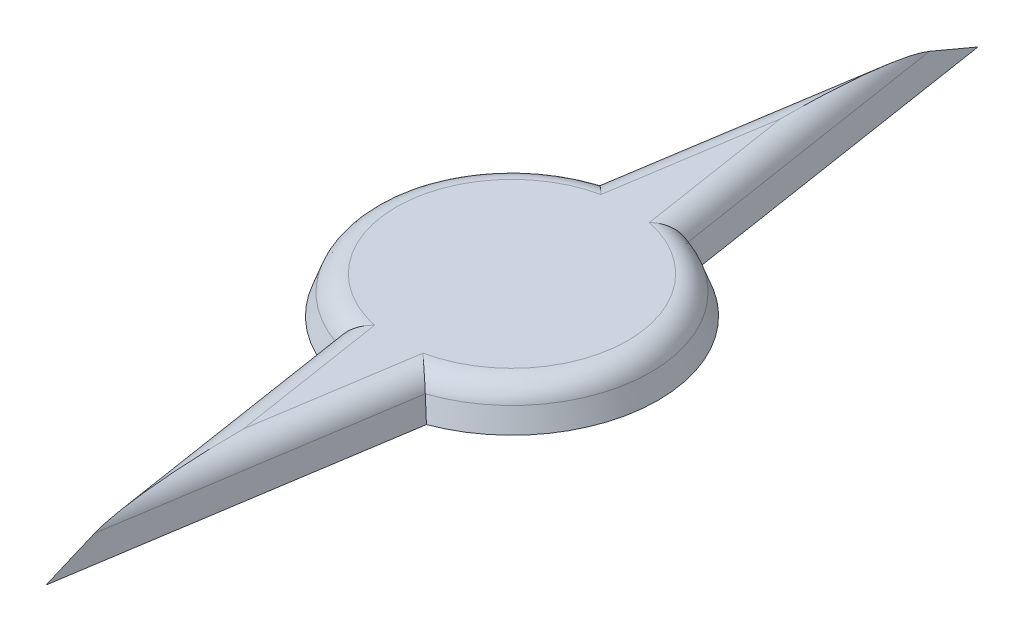
SolidWorks part; units mm, degrees
material "ABS"
ref_plane "Front Plane" through (0, 0, 0) normal (0, 0, 1) x (1, 0, 0)
ref_plane "Top Plane" through (0, 0, 0) normal (0, 1, 0) x (1, 0, 0)
ref_plane "Right Plane" through (0, 0, 0) normal (1, 0, 0) x (0, 0, -1)
sketch "Sketch1" plane through (0, 0, 0) normal (0, 1, 0) x (1, 0, 0)
  line L0 (0, 0) -> (0, 19.1379) construction
  line L1 (0, 19.1379) -> (-2.105, 5.6186)
  line L2 (0, 19.1379) -> (2.105, 5.6186)
  line L3 (-17.7825, 0) -> (16.5322, 0) construction
  line L4 (0, -19.1379) -> (2.105, -5.6186)
  line L5 (0, -19.1379) -> (-2.105, -5.6186)
  circle A0 centre (0, 0) radius 6
  point P11 (0, 19.1379)
  dimension "D1" = 12
extrude "Boss-Extrude1" add sketch "Sketch1" along normal blind 1.5 draft 20 contours A0 | A0 L5 L4 | A0 L2 L1
fillet "Fillet1" radius 1 6 edges at (-0.8081, 1.5, 10.3992) (-5.454, 1.5, 0) (-0.8081, 1.5, -10.3992) (0.8081, 1.5, -10.3992) (5.454, 1.5, 0) (0.8081, 1.5, 10.3992)
